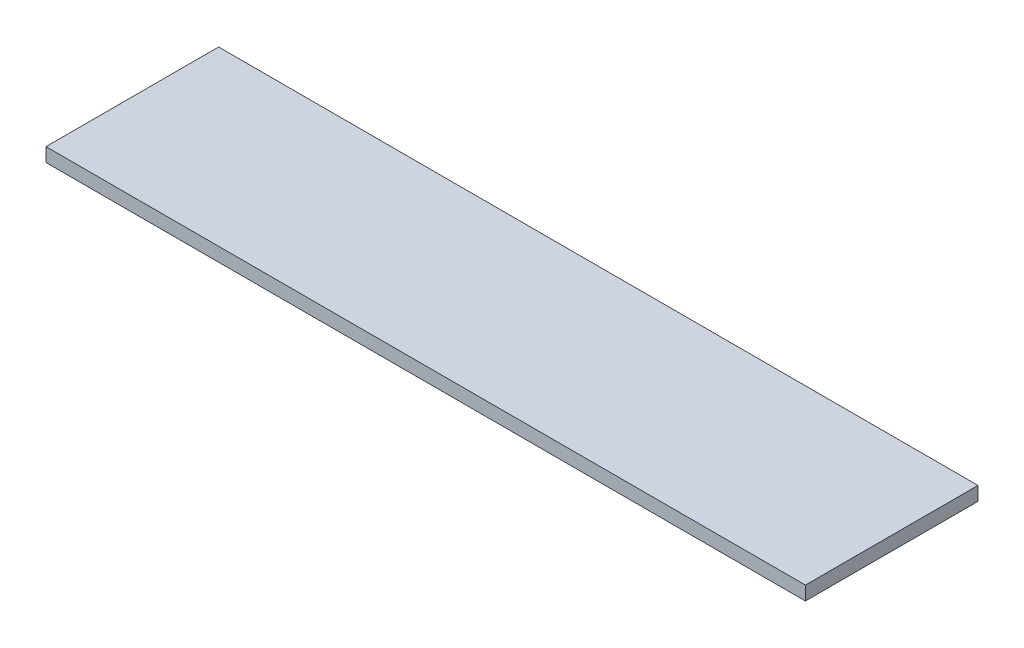
SolidWorks part; units mm, degrees
ref_plane "Front" through (0, 0, 0) normal (0, 0, 1) x (1, 0, 0)
ref_plane "Top" through (0, 0, 0) normal (0, 1, 0) x (1, 0, 0)
ref_plane "Right" through (0, 0, 0) normal (1, 0, 0) x (0, 0, -1)
sketch "Sketch1" plane through (0, 0, 0) normal (1, 0, 0) x (0, 0, -1)
  line L1 (-12.5, 1) -> (12.5, 1)
  line L2 (-12.5, 1) -> (-12.5, -1)
  line L3 (-12.5, -1) -> (12.5, -1)
  line L4 (12.5, 1) -> (12.5, -1)
  line L5 (-12.5, 1) -> (12.5, -1) construction
  line L6 (-12.5, -1) -> (12.5, 1) construction
  point P0 (0, 0)
  dimension "D1" = 25
  dimension "D2" = 2
extrude "Boss-Extrude1" add sketch "Sketch1" along normal blind 110
